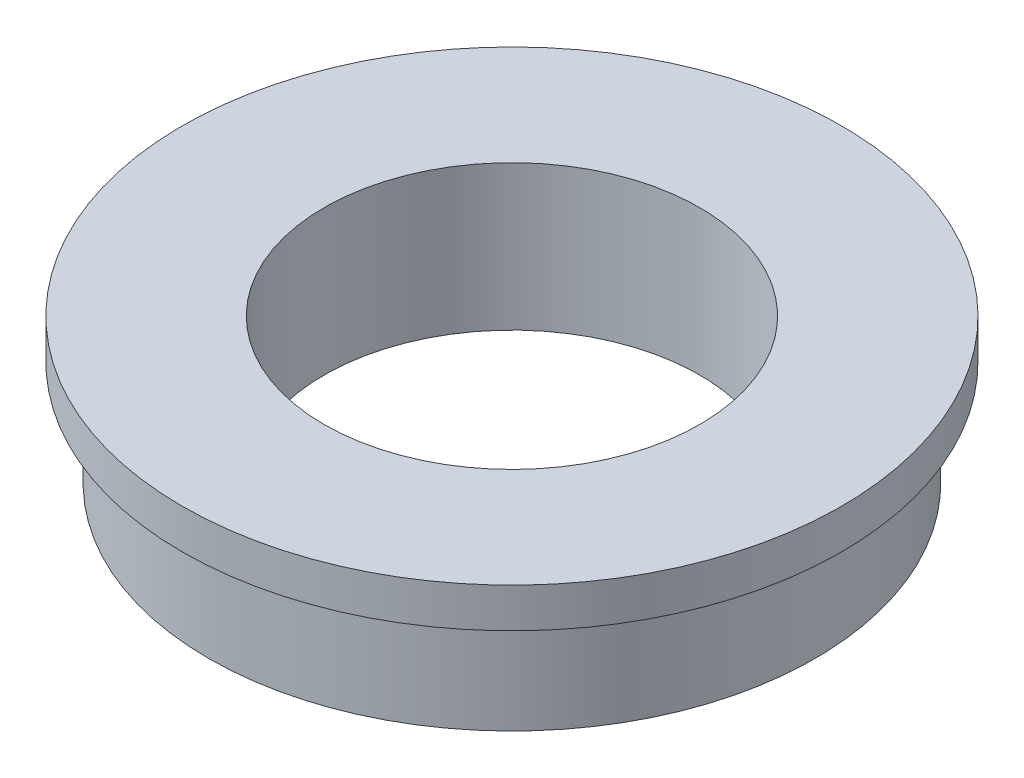
SolidWorks part; units mm, degrees
ref_plane "Plan de face" through (0, 0, 0) normal (0, 0, 1) x (1, 0, 0)
ref_plane "Plan de dessus" through (0, 0, 0) normal (0, 1, 0) x (1, 0, 0)
ref_plane "Plan de droite" through (0, 0, 0) normal (1, 0, 0) x (0, 0, -1)
sketch "Esquisse1" plane through (0, 0, 0) normal (0, 0, 1) x (1, 0, 0)
  line L0 (0, 27.6063) -> (0, -34.4602) construction
  line L1 (-14.25, -8) -> (-14.25, 3)
  line L2 (-14.25, 3) -> (-25, 3)
  line L3 (-25, 3) -> (-25, 0)
  line L4 (-25, 0) -> (-23, 0)
  line L5 (-23, 0) -> (-23, -8)
  line L6 (-23, -8) -> (-14.25, -8)
  dimension "D1" = 28.5
  dimension "D2" = 46
  dimension "D3" = 50
  dimension "D4" = 3
  dimension "D5" = 8
revolve "Révolution1" add sketch "Esquisse1" angle 360 about L0
